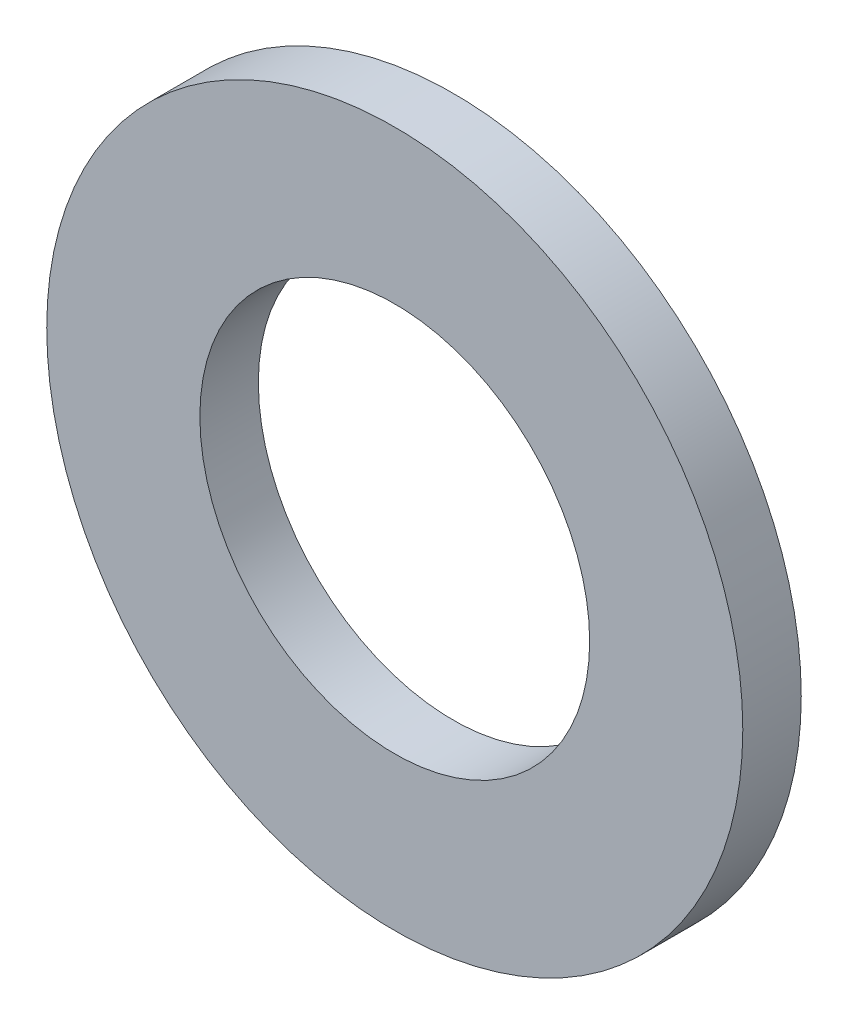
SolidWorks part; units mm, degrees
ref_plane "Front Plane" through (0, 0, 0) normal (0, 0, 1) x (1, 0, 0)
ref_plane "Top Plane" through (0, 0, 0) normal (0, 1, 0) x (1, 0, 0)
ref_plane "Right Plane" through (0, 0, 0) normal (1, 0, 0) x (0, 0, -1)
sketch "Sketch1" plane through (0, 0, 0) normal (0, 0, 1) x (1, 0, 0)
  circle A0 centre (0, 0) radius 7
  circle A1 centre (0, 0) radius 12.5
  dimension "D1" = 14
  dimension "D2" = 25
extrude "Boss-Extrude1" add sketch "Sketch1" along normal blind 2.1
